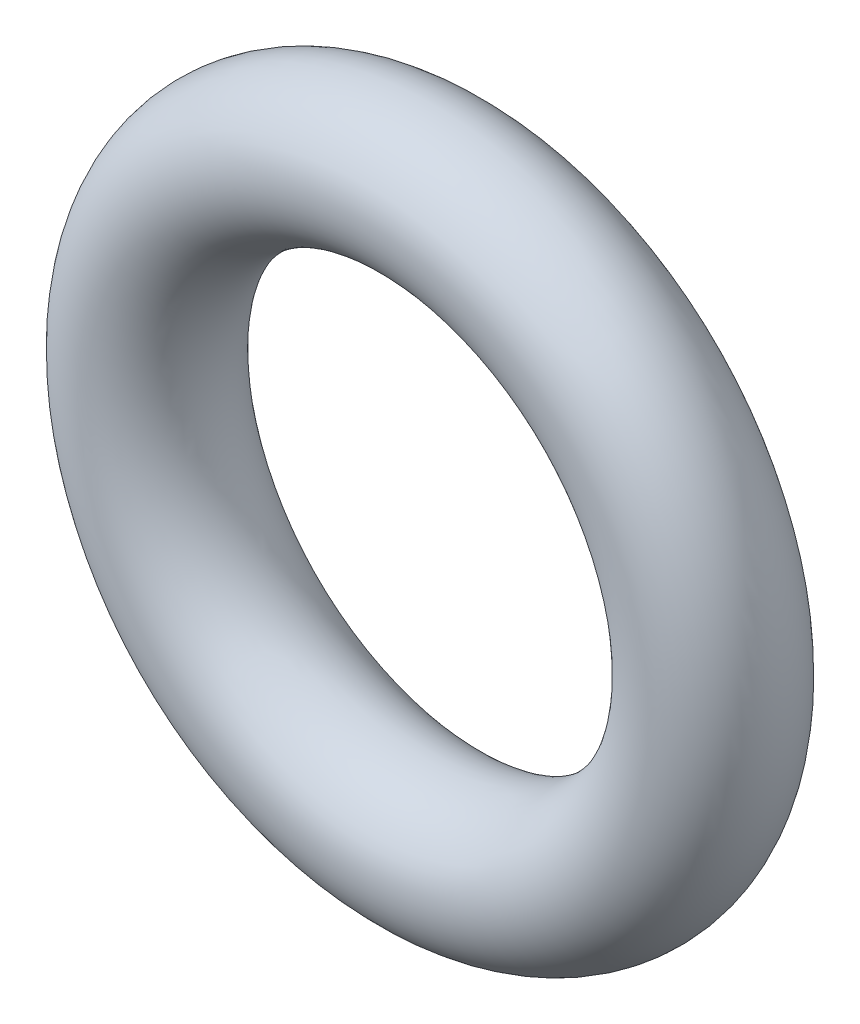
SolidWorks part; units mm, degrees
ref_plane "Front" through (0, 0, 0) normal (0, 0, 1) x (1, 0, 0)
ref_plane "Top" through (0, 0, 0) normal (0, 1, 0) x (1, 0, 0)
ref_plane "Right" through (0, 0, 0) normal (1, 0, 0) x (0, 0, -1)
sketch "Sketch1" plane through (0, 0, 0) normal (1, 0, 0) x (0, -1, 0)
  line L0 (0, -0.889) -> (0, 0.889) construction
  line L2 (-4.8616, 0) -> (4.8616, 0) construction
  line L3 (-2.6416, 0) -> (2.6416, 0) construction
  circle A0 centre (3.5306, 0) radius 0.889
  point P9 (2.6416, 0)
  point P10 (4.4196, 0)
  point P13 (3.5306, 0.889)
  point P14 (3.5306, -0.889)
  dimension "Width" = 1.778
  dimension "ID" = 5.2832
revolve "Revolve1" add sketch "Sketch1" angle 360 about L0
sketch "Sketch2" plane through (0, 0, 0) normal (0, 0, 1) x (1, 0, 0)
  circle A0 centre (0, 0) radius 1.7463
